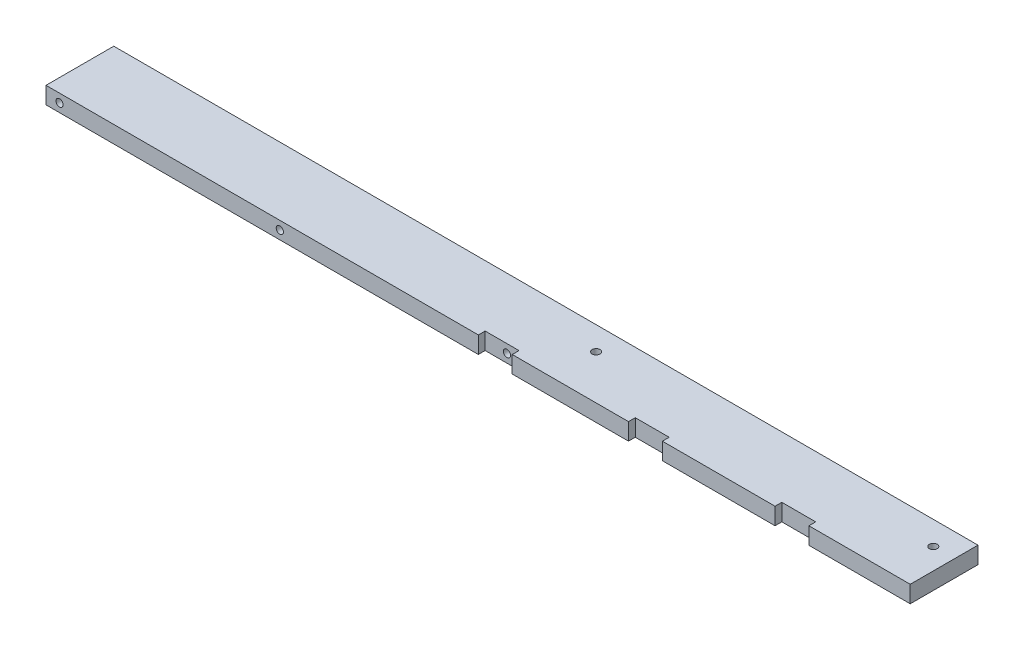
SolidWorks part; units mm, degrees
ref_plane "Front Plane" through (0, 0, 0) normal (0, 0, 1) x (1, 0, 0)
ref_plane "Top Plane" through (0, 0, 0) normal (0, 1, 0) x (1, 0, 0)
ref_plane "Right Plane" through (0, 0, 0) normal (1, 0, 0) x (0, 0, -1)
sketch "Sketch1" plane through (0, 0, 0) normal (1, 0, 0) x (0, 0, -1)
  line L1 (0, 0) -> (25.4, 0)
  line L2 (0, 0) -> (0, 6.35)
  line L3 (0, 6.35) -> (25.4, 6.35)
  line L4 (25.4, 0) -> (25.4, 6.35)
  dimension "D1" = 25.4
  dimension "D2" = 6.35
extrude "Boss-Extrude1" add sketch "Sketch1" along normal blind 323.85
hole_wizard "Tap Drill for #6-32 Tap1" positions "Sketch3" profile "Sketch2" hole size "#6-32" standard "ANSI Inch" end condition through all
sketch "Sketch3" plane through (0, 0, 0) normal (0, 0, 1) x (1, 0, 0)
  line L0 (0, 6.35) -> (0, 0) construction
  line L1 (0, 3.175) -> (323.85, 3.175) construction
  line L2 (323.85, 6.35) -> (323.85, 0) construction
  point P0 (5.08, 3.175)
  point P2 (87.63, 3.175)
  point P4 (170.18, 3.175)
  point P7 (0, 3.175)
  dimension "D1" = 5.08
  dimension "D2" = 82.55
  dimension "D3" = 82.55
sketch "Sketch2" plane through (5.08, 3.175, 0) normal (1, 0, 0) x (0, -1, 0)
  line L0 (0, 0) -> (0, 25.4)
  line L1 (0, 25.4) -> (1.3525, 25.4)
  line L2 (1.3525, 25.4) -> (1.3525, 0)
  line L5 (1.3525, 0) -> (0, 0)
  line L11 (0, -6.35) -> (0, 107.95) construction
  dimension "Thru Hole Dia." = 2.7051
  dimension "Thru Hole Depth" = 25.4
hole_wizard "CBORE for #4 Binding Head Machine Screw2" positions "Sketch5" profile "Sketch4" counterbore size "#4" standard "ANSI Inch" end condition through all
sketch "Sketch5" plane through (0, 0, 0) normal (0, -1, 0) x (-1, 0, 0)
  line L2 (-323.85, 25.4) -> (0, 25.4) construction
  line L3 (0, 0) -> (0, 25.4) construction
  point P0 (-315.9125, 16.5862)
  point P8 (-189.5475, 16.5862)
  dimension "D1" = 189.5475
  dimension "D2" = 8.8138
  dimension "D3" = 126.365
  dimension "D4" = 8.8138
sketch "Sketch4" plane through (315.9125, 0, -16.5862) normal (1, 0, 0) x (0, 0, -1)
  line L0 (0, 0) -> (0, 6.35)
  line L1 (0, 6.35) -> (1.4732, 6.35)
  line L3 (1.4732, 6.35) -> (1.4732, 2.8448)
  line L4 (1.4732, 2.8448) -> (2.4003, 2.8448)
  line L5 (2.4003, 2.8448) -> (2.4003, 0)
  line L7 (2.4003, 0) -> (0, 0)
  line L11 (0, -6.35) -> (0, 107.95) construction
  dimension "Thru Hole Dia." = 2.9464
  dimension "Thru Hole Depth" = 6.35
  dimension "C'Bore Dia." = 4.8006
  dimension "C'Bore Depth" = 2.8448
extrude "Cut-Extrude2" cut sketch "Sketch7" against normal blind 2.54
sketch "Sketch7" plane through (405.6725, 78.178, 0) normal (0, 0, 1) x (0, 1, 0)
  line L1 (-85.2248, 243.6561) -> (-68.7025, 243.6561)
  line L2 (-85.2248, 243.6561) -> (-85.2248, 230.9561)
  line L3 (-85.2248, 230.9561) -> (-68.7025, 230.9561)
  line L4 (-68.7025, 243.6561) -> (-68.7025, 230.9561)
  line L7 (-84.7833, 187.3945) -> (-69.398, 187.3945)
  line L8 (-84.7833, 187.3945) -> (-84.7833, 174.6945)
  line L9 (-84.7833, 174.6945) -> (-69.398, 174.6945)
  line L10 (-69.398, 187.3945) -> (-69.398, 174.6945)
  line L13 (-84.7833, 132.4794) -> (-69.398, 132.4794)
  line L14 (-84.7833, 132.4794) -> (-84.7833, 119.7794)
  line L15 (-84.7833, 119.7794) -> (-69.398, 119.7794)
  line L16 (-69.398, 132.4794) -> (-69.398, 119.7794)
  dimension "D1" = 12.7
  dimension "D2" = 12.7
  dimension "D3" = 12.7
